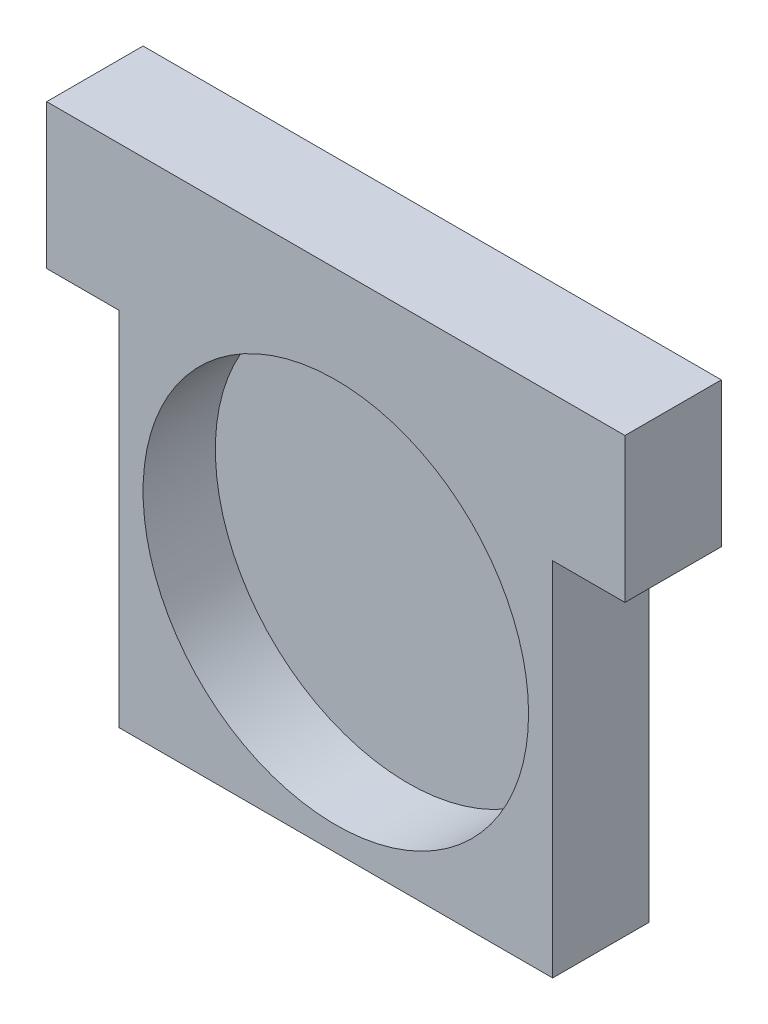
SolidWorks part; units mm, degrees
ref_plane "Front Plane" through (0, 0, 0) normal (0, 0, 1) x (1, 0, 0)
ref_plane "Top Plane" through (0, 0, 0) normal (0, 1, 0) x (1, 0, 0)
ref_plane "Right Plane" through (0, 0, 0) normal (1, 0, 0) x (0, 0, -1)
sketch "Sketch1" plane through (0, 0, 0) normal (0, 0, 1) x (1, 0, 0)
  line L1 (-38.1, 38.1) -> (38.1, 38.1)
  line L2 (-38.1, 38.1) -> (-38.1, -38.1)
  line L3 (-38.1, -38.1) -> (38.1, -38.1)
  line L4 (38.1, 38.1) -> (38.1, -38.1)
  line L5 (-38.1, 38.1) -> (38.1, -38.1) construction
  line L6 (-38.1, -38.1) -> (38.1, 38.1) construction
  point P0 (0, 0)
  dimension "D1" = 76.2
  dimension "D2" = 76.2
extrude "Boss-Extrude1" add sketch "Sketch1" along normal blind 12.7
sketch "Sketch2" plane through (0, 0, 12.7) normal (0, 0, 1) x (1, 0, 0)
  circle A0 centre (0, 0) radius 25.4
  dimension "D1" = 50.8
extrude "Cut-Extrude1" cut sketch "Sketch2" against normal blind 9.525
sketch "Sketch3" plane through (0, 0, 12.7) normal (0, 0, 1) x (1, 0, 0)
  line L0 (38.1, 19.05) -> (28.575, 19.05)
  line L1 (38.1, -38.1) -> (38.1, 38.1) construction
  line L2 (28.575, 19.05) -> (28.575, -28.575)
  line L3 (28.575, -28.575) -> (-28.575, -28.575)
  line L4 (-28.575, -28.575) -> (-28.575, 19.05)
  line L5 (-28.575, 19.05) -> (-38.1, 19.05)
  line L6 (-38.1, 38.1) -> (-38.1, -38.1) construction
  line L7 (-28.575, 19.05) -> (28.575, 19.05) construction
  line L8 (38.1, 38.1) -> (-38.1, 38.1) construction
  dimension "D1" = 19.05
  dimension "D2" = 66.675
  dimension "D3" = 57.15
extrude "Cut-Extrude3" cut sketch "Sketch3" against normal through all and the other way through all
